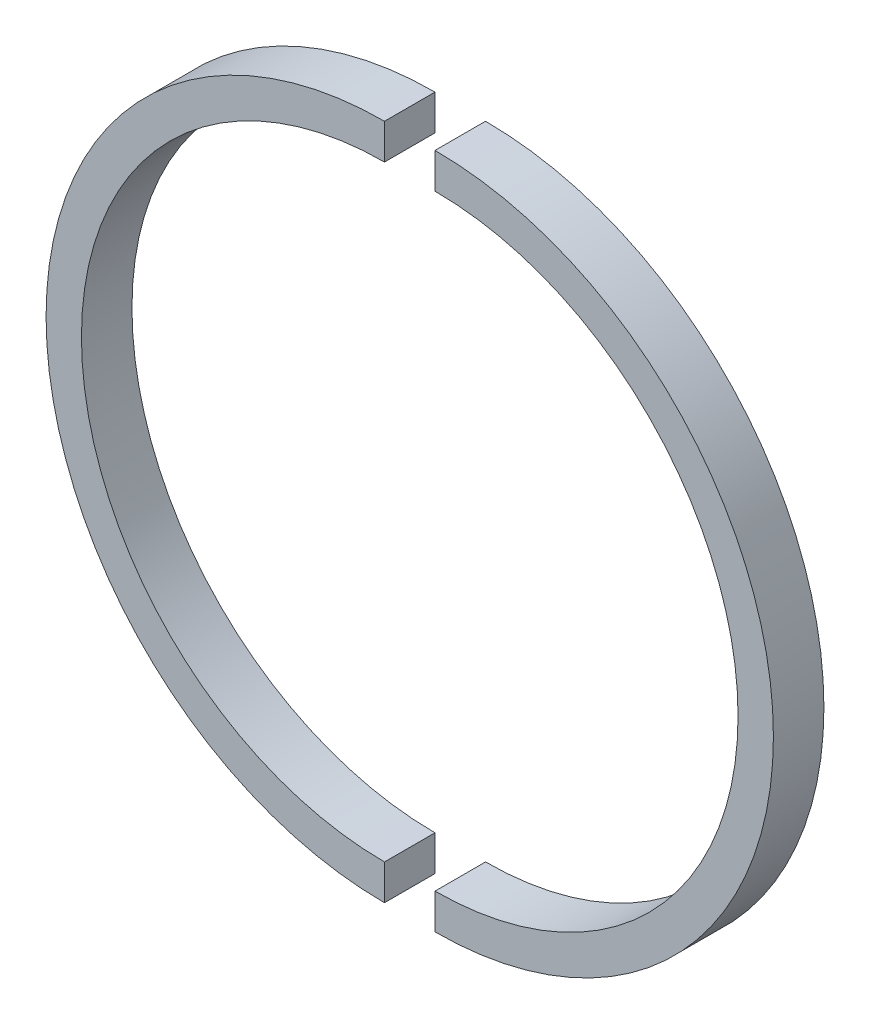
SolidWorks part; units mm, degrees
ref_plane "Front Plane" through (0, 0, 0) normal (0, 0, 1) x (1, 0, 0)
ref_plane "Top Plane" through (0, 0, 0) normal (0, 1, 0) x (1, 0, 0)
ref_plane "Right Plane" through (0, 0, 0) normal (1, 0, 0) x (0, 0, -1)
sketch "Sketch1" plane through (0, 0, 0) normal (1, 0, 0) x (0, 0, -1)
  line L0 (-29.8744, 0) -> (27.9622, 0) construction
  line L1 (-5, 67) -> (5, 67)
  line L2 (-5, 67) -> (-5, 60)
  line L3 (-5, 60) -> (5, 60)
  line L4 (5, 67) -> (5, 60)
  dimension "D1" = 7
  dimension "D2" = 10
  dimension "D3" = 5
  dimension "D4" = 60
revolve "Revolve1" add sketch "Sketch1" angle 180 about L0
sketch "Sketch2" plane through (0, 0, 0) normal (1, 0, 0) x (0, 0, -1)
  line L0 (-5, 67) -> (-5, 60) construction
  line L1 (-5, 60) -> (5, 60) construction
  line L2 (5, 60) -> (5, 67) construction
  line L3 (5, 67) -> (-5, 67) construction
  line L4 (-5, -60) -> (-5, -67) construction
  line L5 (-5, -67) -> (5, -67) construction
  line L6 (5, -67) -> (5, -60) construction
  line L7 (5, -60) -> (-5, -60) construction
  line L8 (-5, 67) -> (-5, 60)
  line L9 (-5, 60) -> (5, 60)
  line L10 (5, 60) -> (5, 67)
  line L11 (5, 67) -> (-5, 67)
  line L12 (-5, -60) -> (-5, -67)
  line L13 (-5, -67) -> (5, -67)
  line L14 (5, -67) -> (5, -60)
  line L15 (5, -60) -> (-5, -60)
sketch "Sketch4" plane through (10, 0, 0) normal (1, 0, 0) x (0, 0, -1)
  line L0 (-23.3477, 0) -> (21.6309, 0) construction
  line L1 (5.5, 0) -> (-5.5, 0) construction
  line L6 (5, 67) -> (-5, 67)
  line L7 (-5, 67) -> (-5, 60)
  line L8 (-5, 60) -> (5, 60)
  line L9 (5, 60) -> (5, 67)
  line L10 (5, 67) -> (-5, 67)
  line L11 (-5, 67) -> (-5, 60)
  line L12 (-5, 60) -> (5, 60)
  line L13 (5, 60) -> (5, 67)
  dimension "D1" = 0
revolve "Revolve3" add sketch "Sketch4" angle 180 about L0
